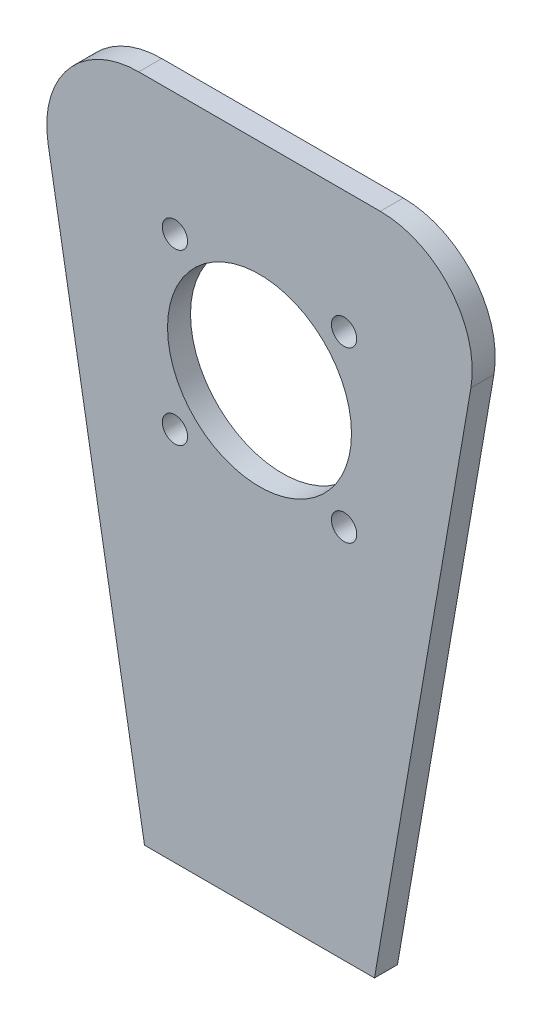
SolidWorks part; units mm, degrees
material "1.0116 (S235J2G3)"
ref_plane "Front Plane" through (0, 0, 0) normal (0, 0, 1) x (1, 0, 0)
ref_plane "Top Plane" through (0, 0, 0) normal (0, 1, 0) x (1, 0, 0)
ref_plane "Right Plane" through (0, 0, 0) normal (1, 0, 0) x (0, 0, -1)
sketch "Sketch1" plane through (0, 0, 0) normal (0, 0, 1) x (1, 0, 0)
  line L0 (0, 0) -> (0, 180.9955) construction
  line L1 (25, 0) -> (-25, 0)
  line L2 (-25, 0) -> (-50, 145)
  line L3 (-50, 145) -> (50, 145)
  line L4 (0, 100) -> (-18.3848, 118.3848) construction
  line L5 (25, 0) -> (50, 145)
  line L6 (-51.8557, 100) -> (83.1032, 100) construction
  circle A0 centre (0, 100) radius 20
  circle A1 centre (0, 100) radius 26 construction
  circle A2 centre (-18.3848, 118.3848) radius 2.75
  circle A3 centre (-18.3848, 81.6152) radius 2.75
  circle A4 centre (18.3848, 81.6152) radius 2.75
  circle A5 centre (18.3848, 118.3848) radius 2.75
  point P12 (0, 145)
  dimension "D2" = 40
  dimension "D5" = 45
  dimension "D6" = 52
  dimension "D7" = 5.5
  dimension "D1" = 145
  dimension "D3" = 25
  dimension "D4" = 50
  dimension "D8" = 45
  dimension "D9" = 100
extrude "Boss-Extrude1" add sketch "Sketch1" along normal blind 5
fillet "Fillet1" radius 20 2 edges at (-50, 145, 2.5) (50, 145, 2.5)
